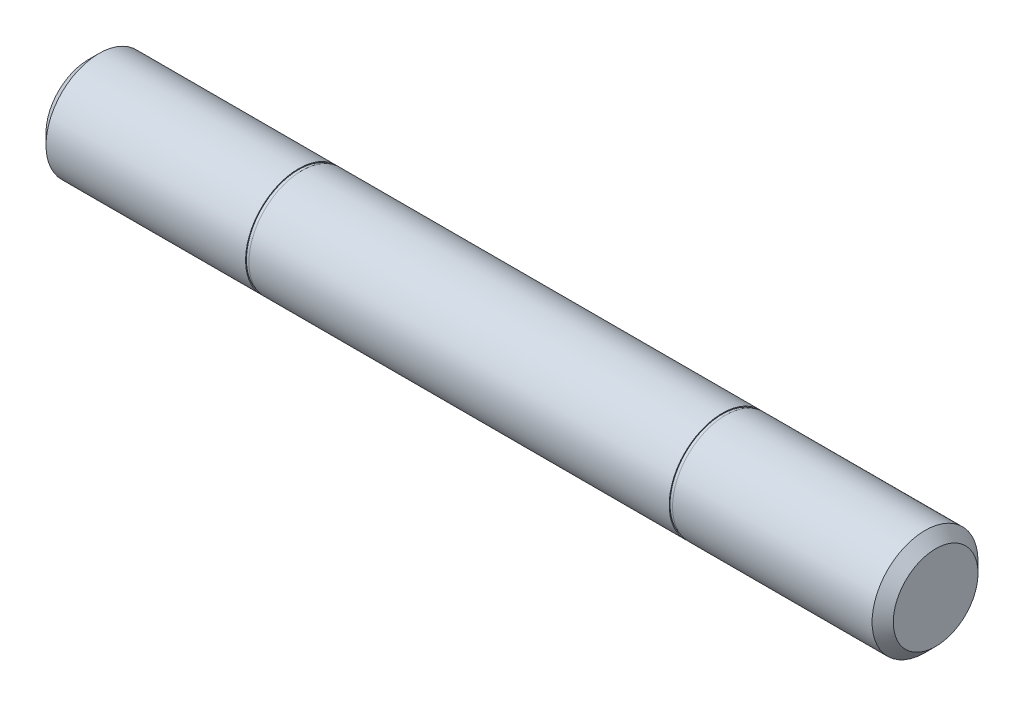
SolidWorks part; units mm, degrees
ref_plane "Front Plane" through (0, 0, 0) normal (0, 0, 1) x (1, 0, 0)
ref_plane "Top Plane" through (0, 0, 0) normal (0, 1, 0) x (1, 0, 0)
ref_plane "Right Plane" through (0, 0, 0) normal (1, 0, 0) x (0, 0, -1)
sketch "Sketch1" plane through (0, 0, 0) normal (0, 0, 1) x (1, 0, 0)
  line L0 (-12.7, 0) -> (12.7, 0) construction
  line L1 (-12.7, 1.5875) -> (-12.7, -1.5875) construction
  line L2 (12.7, 1.5875) -> (12.7, -1.5875) construction
  dimension "Diameter" = 3.175
  dimension "Length" = 25.4
sketch "Sketch2" plane through (0, 0, 0) normal (1, 0, 0) x (0, 0, -1)
  circle A0 centre (0, 0) radius 1.5875
extrude "Extrude1" add sketch "Sketch2" against normal up to vertex (12.7 mm away) and the other way up to vertex (12.7 mm away) up to point (-12.7, 0, 0) other way up to point (12.7, 0, 0)
chamfer "Chamfer1" distance 0.3175 angle 45 2 edges at (12.7, 0, -1.5875) (-12.7, 0, -1.5875)
sketch "Sketch3" plane through (0, 0, 0) normal (1, 0, 0) x (0, 0, -1)
  circle A0 centre (0, 0) radius 1.5875 construction
  circle A1 centre (0, 0) radius 1.5875
  circle A2 centre (0, 0) radius 1.5621
  dimension "D1" = 0.0254
ref_plane "Plane1" through (-6.35, 0, 0) normal (-1, 0, 0) x (0, 0, 1)
ref_plane "Plane2" through (6.35, 0, 0) normal (1, 0, 0) x (0, 0, -1)
sketch "Sketch4" plane through (-6.35, 0, 0) normal (-1, 0, 0) x (0, 0, 1)
  circle A0 centre (0, 0) radius 1.5875 construction
  circle A1 centre (0, 0) radius 1.5621 construction
  circle A2 centre (0, 0) radius 1.5875
  circle A3 centre (0, 0) radius 1.5621
extrude "Cut-Extrude2" cut sketch "Sketch4" against normal mid plane 0.1
sketch "Sketch5" plane through (6.35, 0, 0) normal (1, 0, 0) x (0, 0, -1)
  circle A0 centre (0, 0) radius 1.5621 construction
  circle A1 centre (0, 0) radius 1.5875 construction
  circle A2 centre (0, 0) radius 1.5621
  circle A3 centre (0, 0) radius 1.5875
extrude "Cut-Extrude3" cut sketch "Sketch5" against normal mid plane 0.1
equation "\"D1@Chamfer1\" = \"Diameter@Sketch1\"*.1"
